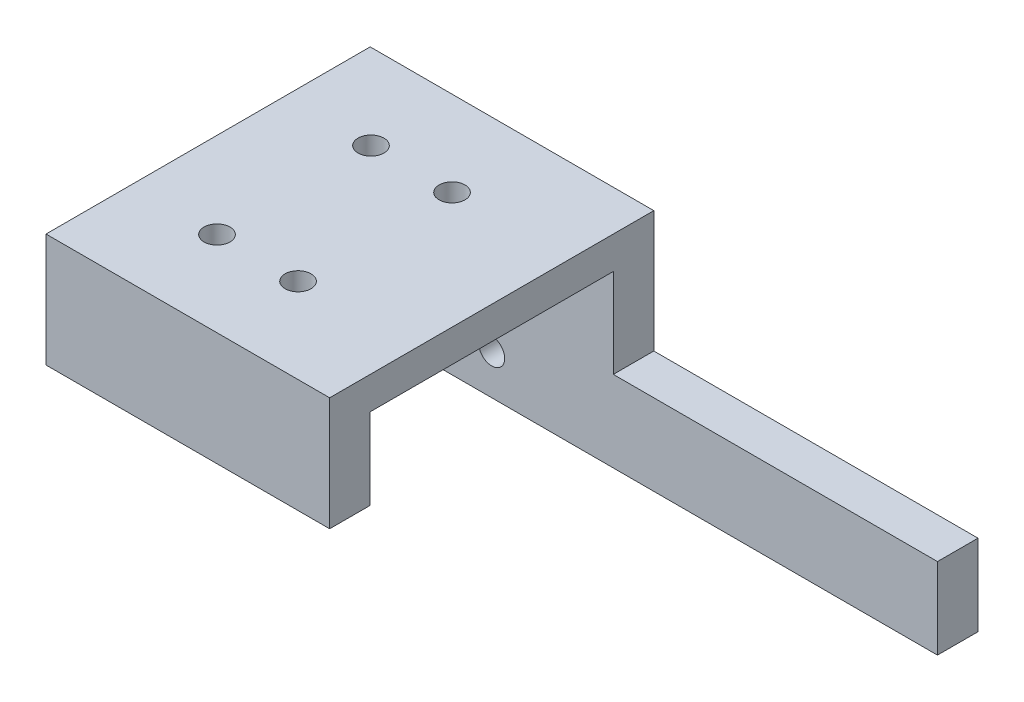
SolidWorks part; units mm, degrees
ref_plane "前视基准面" through (0, 0, 0) normal (0, 0, 1) x (1, 0, 0)
ref_plane "上视基准面" through (0, 0, 0) normal (0, 1, 0) x (1, 0, 0)
ref_plane "右视基准面" through (0, 0, 0) normal (1, 0, 0) x (0, 0, -1)
sketch "草图1" plane through (0, 0, 0) normal (0, 1, 0) x (1, 0, 0)
  line L1 (0, 0) -> (35, 0)
  line L2 (0, 0) -> (0, 40)
  line L3 (0, 40) -> (35, 40)
  line L4 (35, 0) -> (35, 40)
  dimension "D1" = 40
  dimension "D2" = 35
extrude "凸台-拉伸1" add sketch "草图1" along normal blind 4
sketch "草图2" plane through (0, 4, 0) normal (0, 1, 0) x (1, 0, 0)
  line L1 (0, 0) -> (35, 0) construction
  line L3 (0, 20) -> (35, 20) construction
  line L4 (0, 40) -> (0, 0) construction
  circle A0 centre (10.6, 29.5) radius 1.6
  circle A1 centre (20.6, 29.5) radius 1.6
  circle A2 centre (20.6, 10.5) radius 1.6
  circle A3 centre (10.6, 10.5) radius 1.6
  dimension "D3" = 3.2
  dimension "D1" = 10.6
  dimension "D2" = 9.5
  dimension "D4" = 10
  dimension "D5" = 20
extrude "切除-拉伸1" cut sketch "草图2" against normal blind 6
sketch "草图3" plane through (0, 0, 0) normal (0, -1, 0) x (1, 0, 0)
  line L11 (0, -40) -> (35, -40)
  line L12 (0, -40) -> (0, -35)
  line L13 (0, -35) -> (35, -35)
  line L14 (35, -40) -> (35, -35)
  dimension "D1" = 5
  dimension "D2" = 35
extrude "凸台-拉伸2" add sketch "草图3" along normal blind 21
sketch "草图4" plane through (0, 0, -40) normal (0, 0, -1) x (-1, 0, 0)
  line L1 (0, -21) -> (-35, -21) construction
  line L2 (0, 4) -> (0, -21) construction
  circle A0 centre (-10, -16) radius 1.6
  circle A1 centre (-20, -16) radius 1.6
  dimension "D1" = 3.2
  dimension "D4" = 3.2
  dimension "D2" = 10
  dimension "D3" = 5
  dimension "D5" = 5
  dimension "D6" = 10
extrude "切除-拉伸2" cut sketch "草图4" against normal blind 15
sketch "草图5" plane through (0, 0, -40) normal (0, 0, -1) x (-1, 0, 0)
  circle A0 centre (-20, -16) radius 2.8
  circle A1 centre (-10, -16) radius 2.8
  dimension "D1" = 5.6
  dimension "D2" = 5.6
extrude "切除-拉伸3" cut sketch "草图5" against normal blind 2
sketch "草图6" plane through (0, 0, -40) normal (0, 0, -1) x (-1, 0, 0)
  line L1 (-35, -21) -> (-75, -21)
  line L2 (-35, -21) -> (-35, -11)
  line L3 (-35, -11) -> (-75, -11)
  line L4 (-75, -21) -> (-75, -11)
  dimension "D1" = 10
  dimension "D2" = 40
extrude "凸台-拉伸3" add sketch "草图6" against normal blind 5
sketch "草图7" plane through (0, 0, 0) normal (0, -1, 0) x (1, 0, 0)
  line L0 (35, 0) -> (35, -35) construction
  line L1 (0, 0) -> (35, 0)
  line L2 (0, 0) -> (0, -5)
  line L3 (0, -5) -> (35, -5)
  line L4 (35, 0) -> (35, -5)
  dimension "D1" = 5
extrude "凸台-拉伸4" add sketch "草图7" along normal blind 10
equation "\"20、\"=19"
